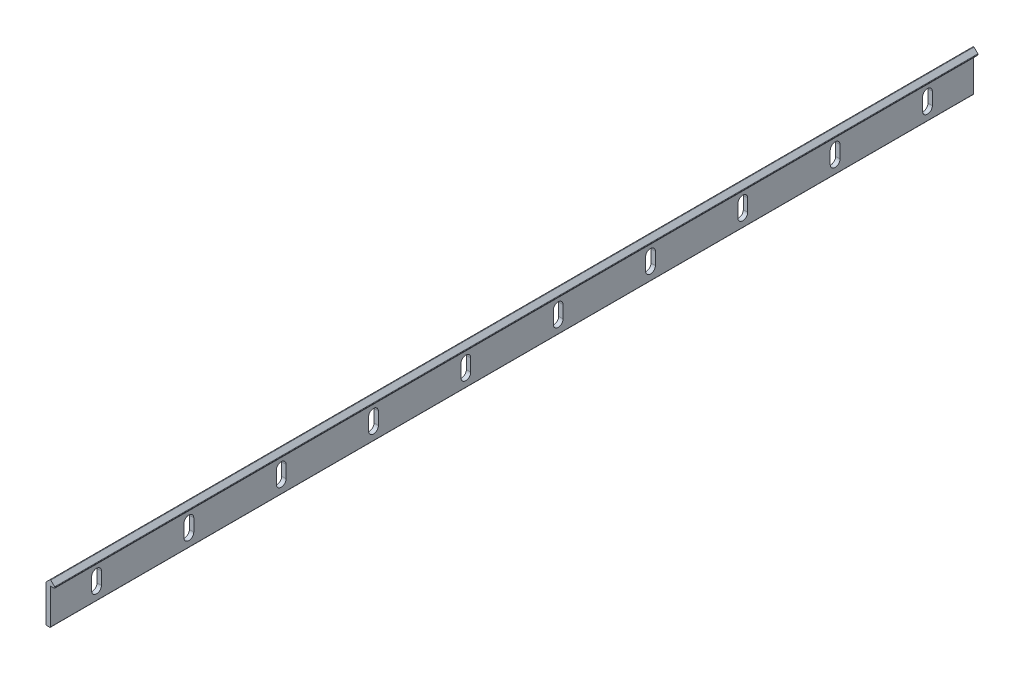
SolidWorks part; units mm, degrees
material "6061-T6 (SS)"
ref_plane "Front Plane" through (0, 0, 0) normal (0, 0, 1) x (1, 0, 0)
ref_plane "Top Plane" through (0, 0, 0) normal (0, 1, 0) x (1, 0, 0)
ref_plane "Right Plane" through (0, 0, 0) normal (1, 0, 0) x (0, 0, -1)
sketch "Sketch1" plane through (0, 0, 0) normal (0, 0, 1) x (1, 0, 0)
  line L0 (0, 0.3) -> (0, 20.125)
  line L1 (0.0879, 20.3371) -> (2.1629, 22.4121)
  line L2 (2.5871, 22.4121) -> (4.6621, 20.3371)
  line L3 (4.75, 20.125) -> (4.75, 19.85)
  line L4 (4.45, 19.55) -> (2.375, 19.55)
  line L5 (2.375, 19.55) -> (2.375, 0.3)
  line L6 (2.075, 0) -> (0.3, 0)
  arc A0 (4.75, 19.85) -> (4.45, 19.55) centre (4.45, 19.85) cw
  arc A1 (4.6621, 20.3371) -> (4.75, 20.125) centre (4.45, 20.125) cw
  arc A2 (0, 20.125) -> (0.0879, 20.3371) centre (0.3, 20.125) cw
  arc A3 (2.1629, 22.4121) -> (2.5871, 22.4121) centre (2.375, 22.2) cw
  arc A4 (0, 0.3) -> (0.3, 0) centre (0.3, 0.3) ccw
  arc A5 (2.375, 0.3) -> (2.075, 0) centre (2.075, 0.3) cw
  point P10 (4.75, 19.55)
  point P13 (4.75, 20.2493)
  point P16 (0, 20.2493)
  point P21 (0, 0)
  point P24 (2.375, 0)
  dimension "D4" = 0.3
  dimension "D6" = 0.3
  dimension "D1" = 2.375
  dimension "D2" = 19.55
  dimension "D3" = 2.375
  dimension "D5" = 22.5
extrude "Boss-Extrude1" add sketch "Sketch1" along normal blind 500
sketch "Sketch2" plane through (2.375, 0, 0) normal (1, 0, 0) x (0, 0, -1)
  line L0 (-25, 12.7) -> (-25, 6) construction
  line L1 (-22.35, 12.7) -> (-22.35, 6)
  line L2 (-27.65, 12.7) -> (-27.65, 6)
  line L3 (0, 0.3) -> (0, 19.55) construction
  line L4 (-500, 0) -> (0, 0) construction
  arc A0 (-22.35, 12.7) -> (-27.65, 12.7) centre (-25, 12.7) ccw
  arc A1 (-27.65, 6) -> (-22.35, 6) centre (-25, 6) ccw
  point P2 (-25, 9.35)
  dimension "D1" = 25
  dimension "D2" = 5.3
  dimension "D3" = 6.7
  dimension "D4" = 6
extrude "Cut-Extrude1" cut sketch "Sketch2" against normal through all
pattern_linear "LPattern1" count 10 spacing 50 along (0, 0, 1) of "Cut-Extrude1"
